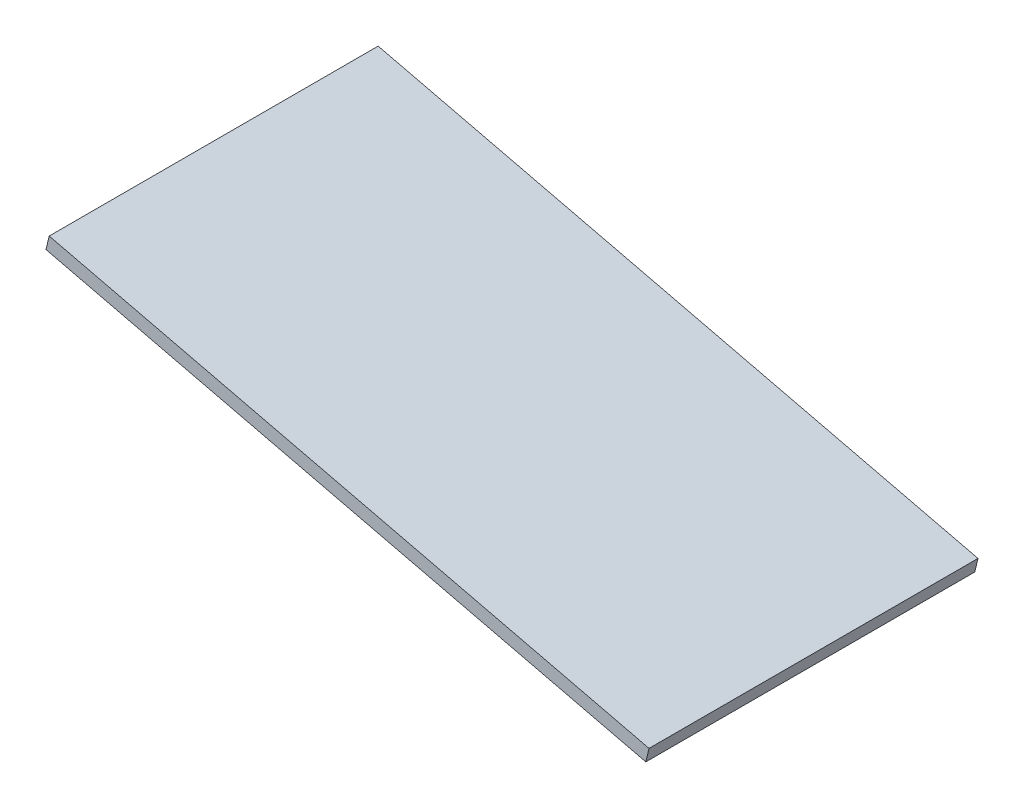
SolidWorks part; units mm, degrees
ref_plane "Front Plane" through (0, 0, 0) normal (0, 0, 1) x (1, 0, 0)
ref_plane "Top Plane" through (0, 0, 0) normal (0, 1, 0) x (1, 0, 0)
ref_plane "Right Plane" through (0, 0, 0) normal (1, 0, 0) x (0, 0, -1)
sketch "Sketch2" plane through (0, 0, 0) normal (0, 0, 1) x (1, 0, 0)
  line L0 (-91.8553, 555.6736) -> (-91.156, 558.591)
  line L1 (-91.8553, 555.6736) -> (39.4262, 524.2066)
  line L2 (-91.156, 558.591) -> (40.1255, 527.1239)
  line L3 (39.4262, 524.2066) -> (40.1255, 527.1239)
  dimension "D1" = 3
extrude "Boss-Extrude1" add sketch "Sketch2" along normal blind 72
